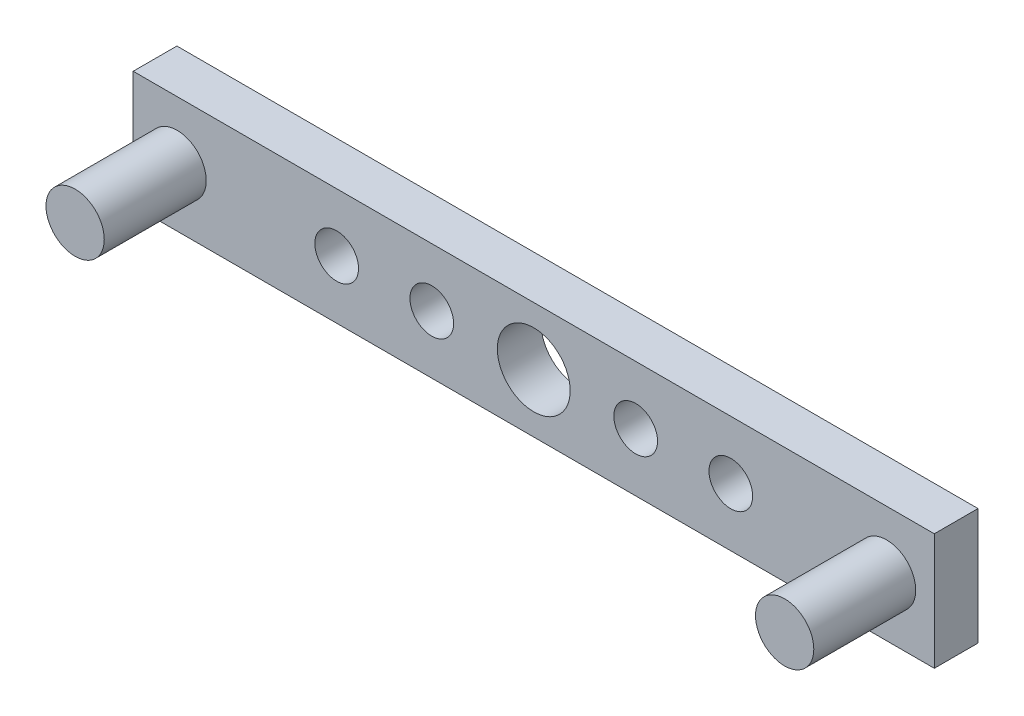
SolidWorks part; units mm, degrees
ref_plane "Front Plane" through (0, 0, 0) normal (0, 0, 1) x (1, 0, 0)
ref_plane "Top Plane" through (0, 0, 0) normal (0, 1, 0) x (1, 0, 0)
ref_plane "Right Plane" through (0, 0, 0) normal (1, 0, 0) x (0, 0, -1)
sketch "Sketch1" plane through (0, 0, 0) normal (0, 0, 1) x (1, 0, 0)
  line L1 (0, 0) -> (55, 0)
  line L2 (0, 0) -> (0, 8)
  line L3 (0, 8) -> (55, 8)
  line L4 (55, 0) -> (55, 8)
  dimension "D1" = 8
  dimension "55" = 55
extrude "Boss-Extrude1" add sketch "Sketch1" along normal blind 3
sketch "Sketch2" plane through (0, 0, 3) normal (0, 0, 1) x (1, 0, 0)
  line L0 (55, 8) -> (0, 8) construction
  circle A0 centre (13.97, 4) radius 1.5
  circle A1 centre (20.5, 4) radius 1.5
  circle A3 centre (41.03, 4) radius 1.5
  circle A4 centre (34.5, 4) radius 1.5
  circle A5 centre (27.5, 4) radius 2.5
  point P4 (27.5, 4)
  point P15 (27.5, 8)
  dimension "D1" = 3
  dimension "D2" = 3
  dimension "D3" = 3
  dimension "D4" = 3
  dimension "D5" = 4
  dimension "D10" = 5
  dimension "D6" = 7
  dimension "D7" = 6.53
  dimension "D8" = 7
  dimension "D9" = 6.53
extrude "Cut-Extrude1" cut sketch "Sketch2" against normal through all
sketch "Sketch3" plane through (0, 0, 0) normal (0, 0, 1) x (1, 0, 0)
  line L0 (0, 8) -> (0, 0) construction
  circle A5 centre (51.726, 4) radius 2
  circle A6 centre (3.014, 4) radius 2
  point P0 (0, 4)
  point P1 (3.014, 4)
  point P4 (0, 0)
  dimension "D12" = 4
  dimension "D13" = 4
extrude "Boss-Extrude2" add sketch "Sketch3" along normal blind 10
